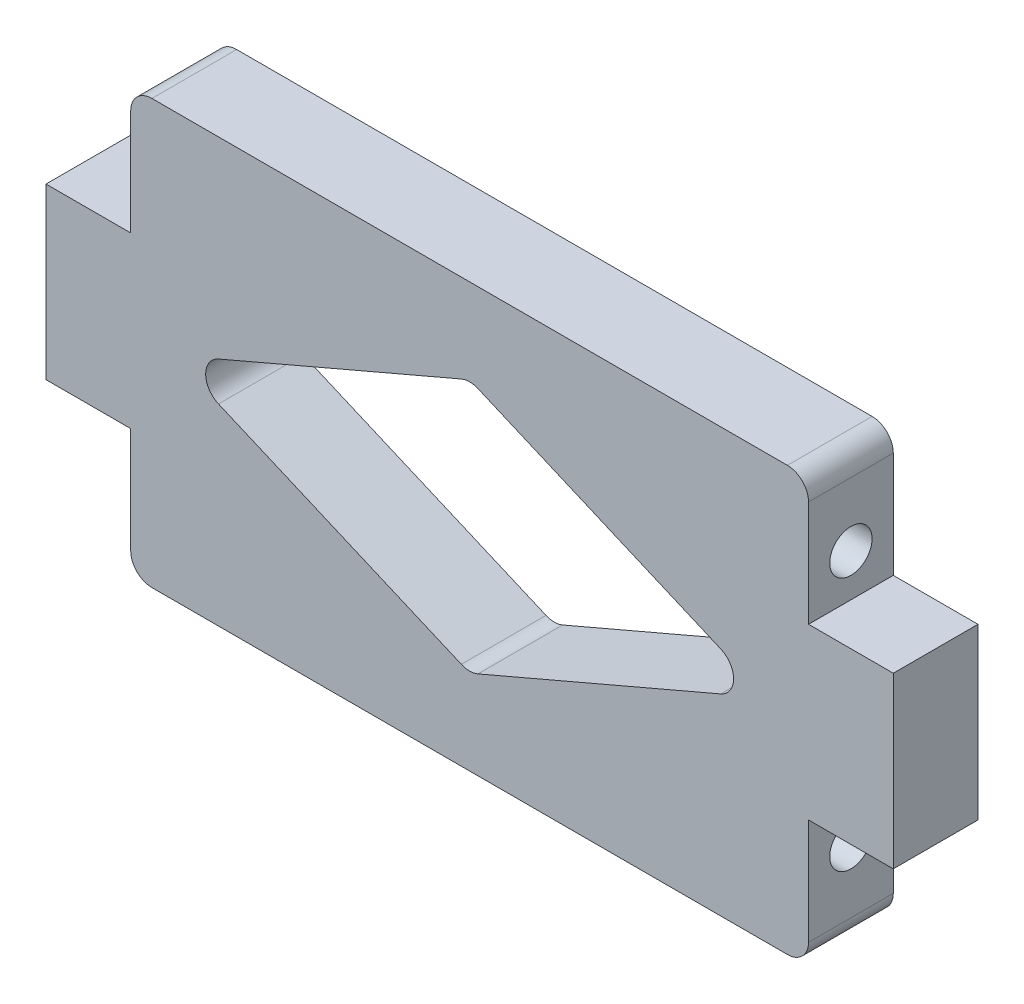
SolidWorks part; units mm, degrees
material "6061-T6 (SS)"
ref_plane "Front Plane" through (0, 0, 0) normal (0, 0, 1) x (1, 0, 0)
ref_plane "Top Plane" through (0, 0, 0) normal (0, 1, 0) x (1, 0, 0)
ref_plane "Right Plane" through (0, 0, 0) normal (1, 0, 0) x (0, 0, -1)
sketch "Sketch1" plane through (0, 0, 0) normal (0, 0, 1) x (1, 0, 0)
  line L0 (0, 0) -> (50.8, 0) construction
  line L1 (-50.8, 31.75) -> (50.8, 31.75)
  line L2 (-50.8, 31.75) -> (-50.8, -31.75)
  line L3 (-50.8, -31.75) -> (50.8, -31.75)
  line L4 (50.8, 31.75) -> (50.8, -31.75)
  line L5 (50.8, 0) -> (63.5, 0) construction
  line L6 (0, 31.75) -> (0, 0) construction
  line L7 (50.8, -12.7) -> (63.5, -12.7)
  line L8 (50.8, -12.7) -> (50.8, 12.7)
  line L9 (50.8, 12.7) -> (63.5, 12.7)
  line L10 (63.5, -12.7) -> (63.5, 12.7)
  line L11 (-50.8, -12.7) -> (-63.5, -12.7)
  line L12 (-50.8, -12.7) -> (-50.8, 12.7)
  line L13 (-50.8, 12.7) -> (-63.5, 12.7)
  line L14 (-63.5, -12.7) -> (-63.5, 12.7)
  dimension "D1" = 50.8
  dimension "D2" = 31.75
  dimension "D3" = 25.4
  dimension "D4" = 12.7
extrude "Boss-Extrude1" add sketch "Sketch1" along normal blind 12.7 contours L14 L11 L2 L13 | L4 L1 L2 L3 | L7 L10 L9 L4
hole_wizard "1/4-20 Tapped Hole1" positions "Sketch3" profile "Sketch2" tap size "1/4-20" standard "ANSI Inch"
sketch "Sketch3" plane through (50.8, 0, 0) normal (1, 0, 0) x (0, 0, -1)
  line L0 (-6.35, 19.05) -> (-6.35, 12.7) construction
  line L1 (-12.7, 12.7) -> (0, 12.7) construction
  line L2 (-6.35, 12.7) -> (-6.35, -12.7) construction
  line L3 (-12.7, -12.7) -> (0, -12.7) construction
  line L4 (-6.35, -12.7) -> (-6.35, -19.05) construction
  point P0 (-6.35, 19.05)
  point P2 (-6.35, -19.05)
  dimension "D1" = 38.1
sketch "Sketch2" plane through (50.8, 19.05, 6.35) normal (0, 1, 0) x (0, 0, -1)
  line L0 (0, 0) -> (0, 18.0438)
  line L1 (0, 18.0438) -> (2.5527, 16.51)
  line L2 (2.5527, 16.51) -> (2.5527, 12.7)
  line L3 (2.5527, 12.7) -> (3.175, 12.7)
  line L4 (3.175, 12.7) -> (3.175, 0)
  line L5 (3.175, 0) -> (0, 0)
  line L10 (0, 18.0438) -> (-2.5527, 16.51) construction
  line L11 (0, -6.35) -> (0, 107.95) construction
  dimension "Tap Drill Dia." = 5.1054
  dimension "Tap Drill Depth" = 16.51
  dimension "Thread Major Dia." = 6.35
  dimension "Thread Depth" = 12.7
  dimension "Drill Angle" = 118
mirror "Mirror1" about plane through (0, 0, 0) normal (1, 0, 0) of "1/4-20 Tapped Hole1"
sketch "Sketch4" plane through (0, 0, 12.7) normal (0, 0, 1) x (1, 0, 0)
  line L0 (-44.45, 0) -> (0, 19.05)
  line L1 (0, 19.05) -> (44.45, 0)
  line L2 (44.45, 0) -> (0, -19.05)
  line L3 (0, -19.05) -> (-44.45, 0)
  line L4 (0, 19.05) -> (0, 0) construction
  line L5 (0, 0) -> (44.45, 0) construction
  line L6 (0, -19.05) -> (0, 0) construction
  line L7 (0, 0) -> (-44.45, 0) construction
  dimension "D1" = 19.05
  dimension "D2" = 44.45
extrude "Cut-Extrude1" cut sketch "Sketch4" against normal through all
fillet "Fillet1" radius 3.175 4 edges at (0, -19.05, 6.35) (0, 19.05, 6.35) (44.45, 0, 6.35) (-44.45, 0, 6.35)
fillet "Fillet2" radius 3.175 4 edges at (-50.8, -31.75, 6.35) (50.8, -31.75, 6.35) (50.8, 31.75, 6.35) (-50.8, 31.75, 6.35)
